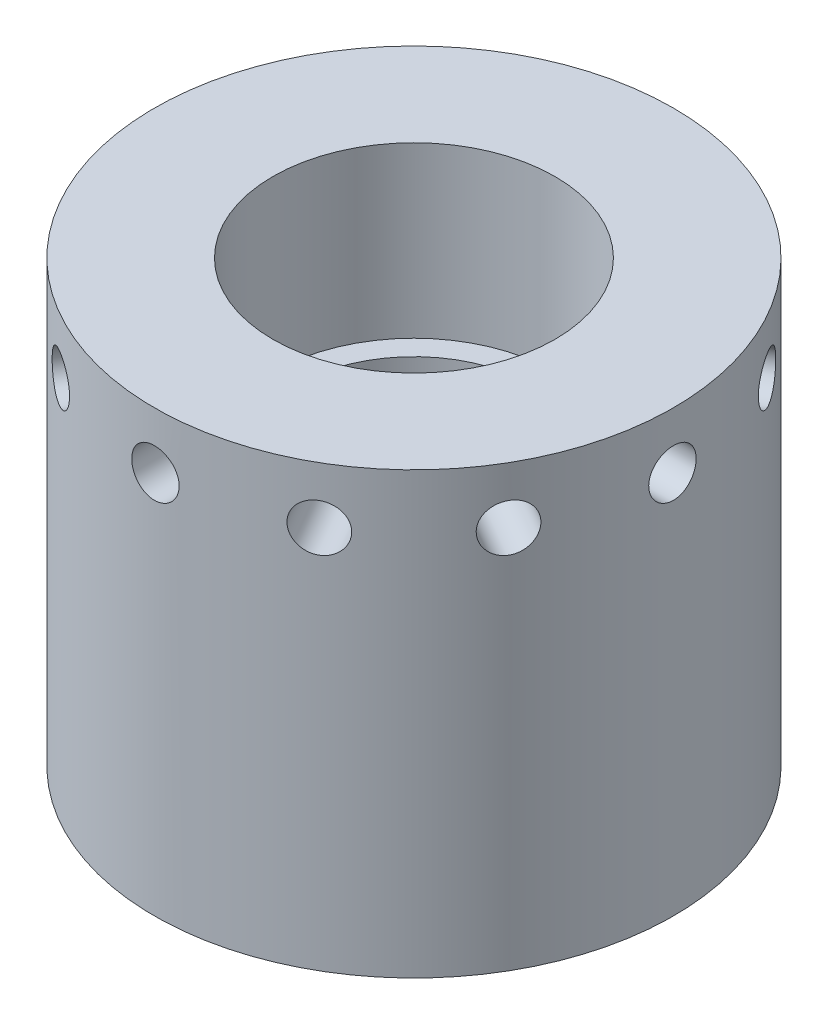
SolidWorks part; units mm, degrees
material "6061-T6 (SS)"
ref_plane "Front Plane" through (0, 0, 0) normal (0, 0, 1) x (1, 0, 0)
ref_plane "Top Plane" through (0, 0, 0) normal (0, 1, 0) x (1, 0, 0)
ref_plane "Right Plane" through (0, 0, 0) normal (1, 0, 0) x (0, 0, -1)
sketch "Sketch1" plane through (0, 0, 0) normal (0, 0, 1) x (1, 0, 0)
  line L1 (12.5, 39) -> (23, 39)
  line L2 (23, 39) -> (23, 0)
  line L3 (23, 0) -> (10.5, 0)
  line L4 (12.5, 39) -> (12.5, 24)
  line L5 (12.5, 24) -> (10.5, 24)
  line L6 (0, 64.1506) -> (0, 68.9776) construction
  line L7 (10.5, 24) -> (10.5, 0)
  line L12 (10.5, 17) -> (17, 17) construction
  line L13 (17, 17) -> (17, 0) construction
  line L17 (15, 17) -> (15, 21) construction
  line L18 (15, 21) -> (10.5, 21) construction
  line L19 (1, 17) -> (1, 0) construction
  point P2 (1, 17)
  point P5 (1, 0)
  point P15 (0, 0)
  point P18 (0, 0)
  point P19 (0, 0)
  point P20 (1, 2.1558)
  point P22 (0, 0)
  dimension "D1" = 25
  dimension "D2" = 15
  dimension "D3" = 2
  dimension "D4" = 2
  dimension "D5" = 17
  dimension "D6" = 6
  dimension "D7" = 16
  dimension "D9" = 4
  dimension "D10" = 3
  dimension "D11" = 1
revolve "Revolve1" add sketch "Sketch1" angle 360 about L6
sketch "Sketch2" plane through (0, 0, 0) normal (0, 0, 1) x (1, 0, 0)
  line L20 (15, 21) -> (1, 21)
  line L21 (15, 17) -> (17, 17)
  line L22 (1, 17) -> (1, 0)
  line L23 (1, 0) -> (17, 0)
  line L24 (17, 17) -> (17, 0)
  line L25 (1, 21) -> (1, 17)
  line L26 (15, 21) -> (15, 17)
revolve "Cut-Revolve1" cut sketch "Sketch2" angle 360 about L22
sketch "Sketch6" plane through (-46.3116, 0, 0) normal (0, 1, 0) x (-1, 0, 0)
  line L0 (-47.3116, 0) -> (-47.3116, 18.5) construction
  circle A2 centre (-47.3116, 18.5) radius 2.5 construction
  circle A3 centre (-47.3116, 18.5) radius 2 construction
  circle A4 centre (-47.3116, 0) radius 16 construction
  circle A5 centre (-47.3116, 0) radius 16
  point P7 (-47.3116, 0.6442)
  dimension "D1" = 0.5
  dimension "D2" = 4
hole_wizard "M4x0.7 Tapped Hole1" positions "Sketch15" profile "Sketch17" tap size "M4x0.7" standard "ANSI Metric"
sketch "Sketch15" plane through (0, 0, 0) normal (0, -1, 0) x (-1, 0, 0)
  point P0 (-1, -18.5)
sketch "Sketch17" plane through (1, 0, 18.5) normal (1, 0, 0) x (0, 0, -1)
  line L0 (0, 0) -> (0, 11.0914)
  line L1 (0, 11.0914) -> (1.65, 10.1)
  line L2 (1.65, 10.1) -> (1.65, 0)
  line L5 (1.65, 0) -> (0, 0)
  line L10 (0, 11.0914) -> (-1.65, 10.1) construction
  line L11 (0, -6.35) -> (0, 107.95) construction
  dimension "Tap Drill Dia." = 3.3
  dimension "Tap Drill Depth" = 10.1
  dimension "Drill Angle" = 118
cosmetic thread "Hole Thread24" parameters "D1"=8, "D2"=4
pattern_circular "CirPattern4" count 6 over 360 about axis through (1, 0, 0) along (0, 1, 0) of "M4x0.7 Tapped Hole1"
cosmetic thread "Hole Thread25"
cosmetic thread "Hole Thread26"
cosmetic thread "Hole Thread27"
cosmetic thread "Hole Thread28"
cosmetic thread "Hole Thread29"
ref_plane "Plane1" through (-23, 0, 0) normal (-1, 0, 0) x (0, 0, 1)
sketch "Sketch12" plane through (-23, 0, 0) normal (-1, 0, 0) x (0, 0, 1)
  line L0 (23, 39) -> (-23, 39) construction
  line L1 (23, 39) -> (-23, 39) construction
  circle A0 centre (0, 34) radius 5 construction
  circle A1 centre (0, 34) radius 2.5 construction
  point P5 (0, 39)
  dimension "D1" = 10
  dimension "D2" = 5
hole_wizard "M5x0.8 Tapped Hole1" positions "Sketch13" profile "Sketch14" tap size "M5x0.8" standard "ANSI Metric"
sketch "Sketch13" plane through (-23, 0, 0) normal (-1, 0, 0) x (0, 0, 1)
  point P0 (0, 34)
sketch "Sketch14" plane through (-23, 34, 0) normal (0, 1, 0) x (0, 0, 1)
  line L0 (0, 0) -> (0, 9.2618)
  line L1 (0, 9.2618) -> (2.1, 8)
  line L2 (2.1, 8) -> (2.1, 0)
  line L5 (2.1, 0) -> (0, 0)
  line L10 (0, 9.2618) -> (-2.1, 8) construction
  line L11 (0, -6.35) -> (0, 107.95) construction
  dimension "Tap Drill Dia." = 4.2
  dimension "Tap Drill Depth" = 8
  dimension "Drill Angle" = 118
cosmetic thread "Hole Thread12"
pattern_circular "CirPattern3" count 12 over 360 about axis through (0, 64.1506, 0) along (0, -1, 0) of "M5x0.8 Tapped Hole1"
cosmetic thread "Hole Thread13"
cosmetic thread "Hole Thread14"
cosmetic thread "Hole Thread15"
cosmetic thread "Hole Thread16"
cosmetic thread "Hole Thread17"
cosmetic thread "Hole Thread18"
cosmetic thread "Hole Thread19"
cosmetic thread "Hole Thread20"
cosmetic thread "Hole Thread21"
cosmetic thread "Hole Thread22"
cosmetic thread "Hole Thread23"
